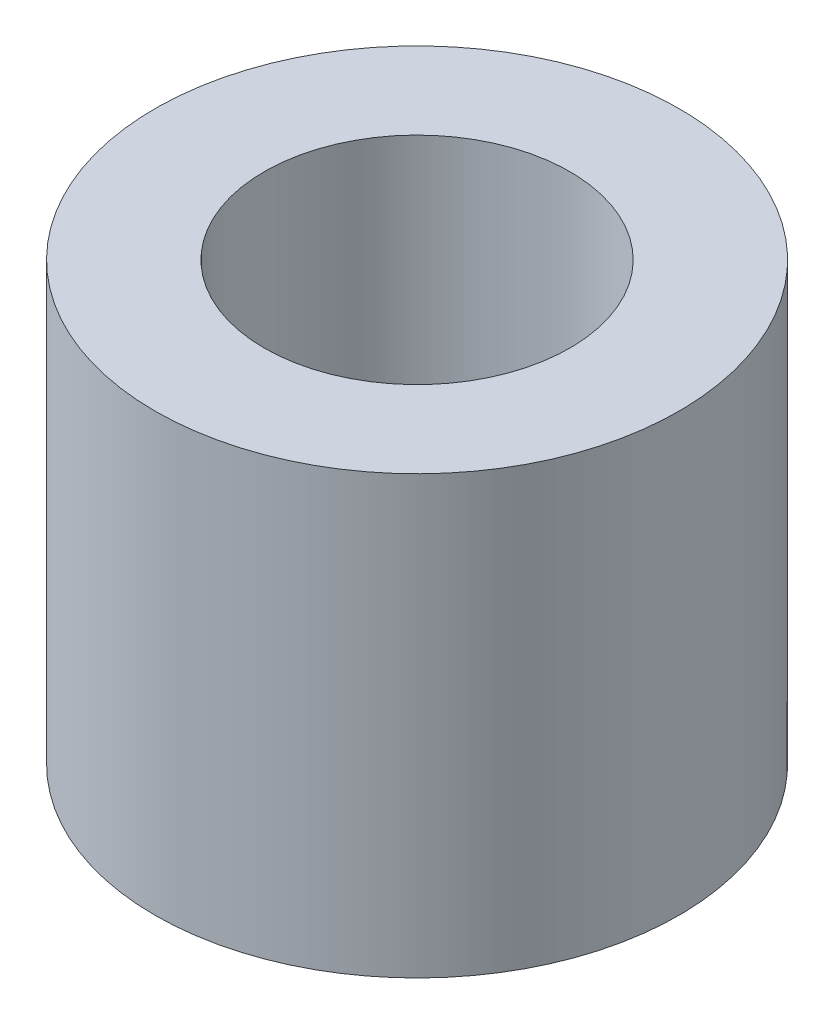
SolidWorks part; units mm, degrees
ref_plane "Front Plane" through (0, 0, 0) normal (0, 0, 1) x (1, 0, 0)
ref_plane "Top Plane" through (0, 0, 0) normal (0, 1, 0) x (1, 0, 0)
ref_plane "Right Plane" through (0, 0, 0) normal (1, 0, 0) x (0, 0, -1)
sketch "Sketch1" plane through (0, 0, 0) normal (0, 1, 0) x (1, 0, 0)
  circle A0 centre (0, 0) radius 3
  circle A1 centre (0, 0) radius 1.75
  dimension "D1" = 6
  dimension "D2" = 3.5
extrude "Boss-Extrude1" add sketch "Sketch1" along normal blind 10
other "Move Face1" face at (0, 0, 3) parameters "D1"=5
other "Move Face2" face at (0, -5, 3) parameters "D1"=10
